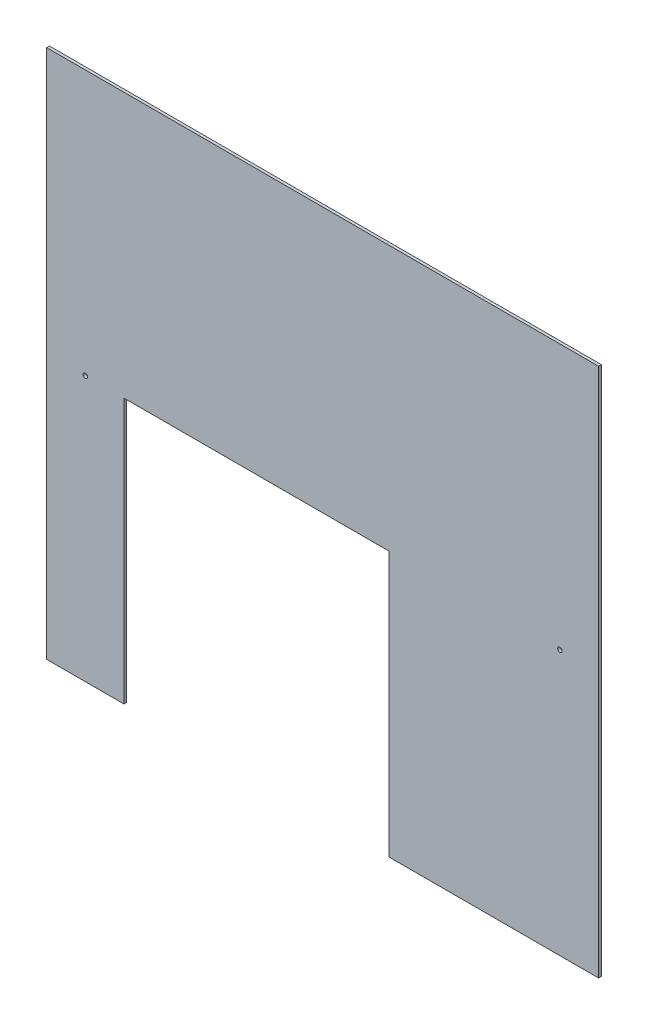
SolidWorks part; units mm, degrees
ref_plane "Front Plane" through (0, 0, 0) normal (0, 0, 1) x (1, 0, 0)
ref_plane "Top Plane" through (0, 0, 0) normal (0, 1, 0) x (1, 0, 0)
ref_plane "Right Plane" through (0, 0, 0) normal (1, 0, 0) x (0, 0, -1)
sketch "Sketch1" plane through (0, 0, 0) normal (0, 0, 1) x (1, 0, 0)
  line L0 (-630.1823, 436.3989) -> (4.8177, 436.3989)
  line L1 (4.8177, 436.3989) -> (4.8177, -173.2011)
  line L7 (-630.1823, -173.2011) -> (-630.1823, 436.3989)
  line L8 (-630.1823, -173.2011) -> (-541.2823, -173.2011)
  line L9 (-541.2823, -173.2011) -> (-541.2823, 131.5989)
  line L10 (-541.2823, 131.5989) -> (-236.4823, 131.5989)
  line L11 (-236.4823, 131.5989) -> (-236.4823, -173.2011)
  line L12 (-236.4823, -173.2011) -> (4.8177, -173.2011)
  dimension "D1" = 609.6
  dimension "D2" = 635
  dimension "D3" = 88.9
  dimension "D4" = 304.8
  dimension "D5" = 304.8
extrude "Boss-Extrude1" add sketch "Sketch1" along normal blind 3.175
sketch "Sketch2" plane through (0, 0, 3.175) normal (0, 0, 1) x (1, 0, 0)
  line L0 (-236.4823, -173.2011) -> (4.8177, -173.2011) construction
  line L1 (-630.1823, -173.2011) -> (-541.2823, -173.2011) construction
  line L2 (-630.1823, 436.3989) -> (-630.1823, -173.2011) construction
  line L3 (4.8177, -173.2011) -> (4.8177, 436.3989) construction
  circle A0 centre (-585.7323, 131.5989) radius 2.5797
  circle A1 centre (-39.6323, 131.5989) radius 2.5797
  dimension "D5" = 5.1594
  dimension "D6" = 5.1594
  dimension "D1" = 304.8
  dimension "D2" = 304.8
  dimension "D3" = 44.45
  dimension "D4" = 44.45
extrude "Cut-Extrude1" cut sketch "Sketch2" against normal blind 3.175
